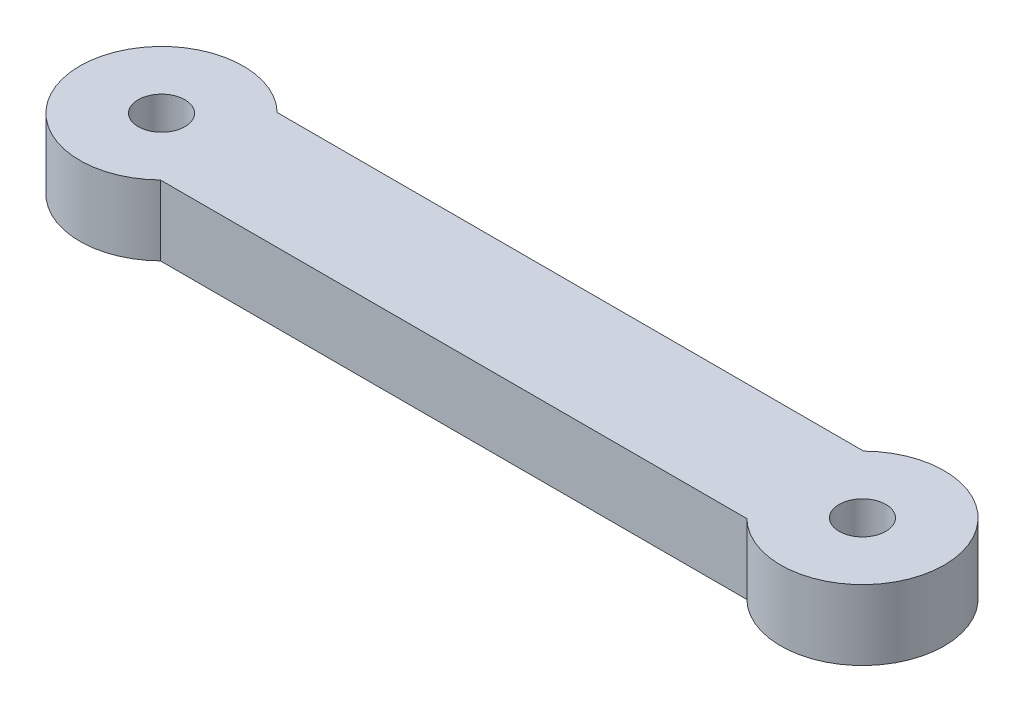
SolidWorks part; units mm, degrees
ref_plane "Alzado" through (0, 0, 0) normal (0, 0, 1) x (1, 0, 0)
ref_plane "Planta" through (0, 0, 0) normal (0, 1, 0) x (1, 0, 0)
ref_plane "Vista lateral" through (0, 0, 0) normal (1, 0, 0) x (0, 0, -1)
sketch "Croquis2" plane through (0, 0, 0) normal (0, 1, 0) x (1, 0, 0)
  line L0 (14.1903, -1.2019) -> (-15.8097, -1.2019) construction
  line L1 (-13.3603, 1.2981) -> (11.7408, 1.2981)
  line L3 (-13.3603, -3.7019) -> (11.7408, -3.7019)
  arc A0 (-13.3603, 1.2981) -> (-13.3603, -3.7019) centre (-15.8097, -1.2019) ccw
  arc A1 (11.7408, -3.7019) -> (11.7408, 1.2981) centre (14.1903, -1.2019) ccw
  circle A2 centre (-15.8097, -1.2019) radius 1
  circle A3 centre (14.1903, -1.2019) radius 1
  point P0 (0, 0)
  dimension "D3" = 2
  dimension "D4" = 7
  dimension "D5" = 7
  dimension "D1" = 5
  dimension "D2" = 30
extrude "Saliente-Extruir1" add sketch "Croquis2" along normal blind 3
